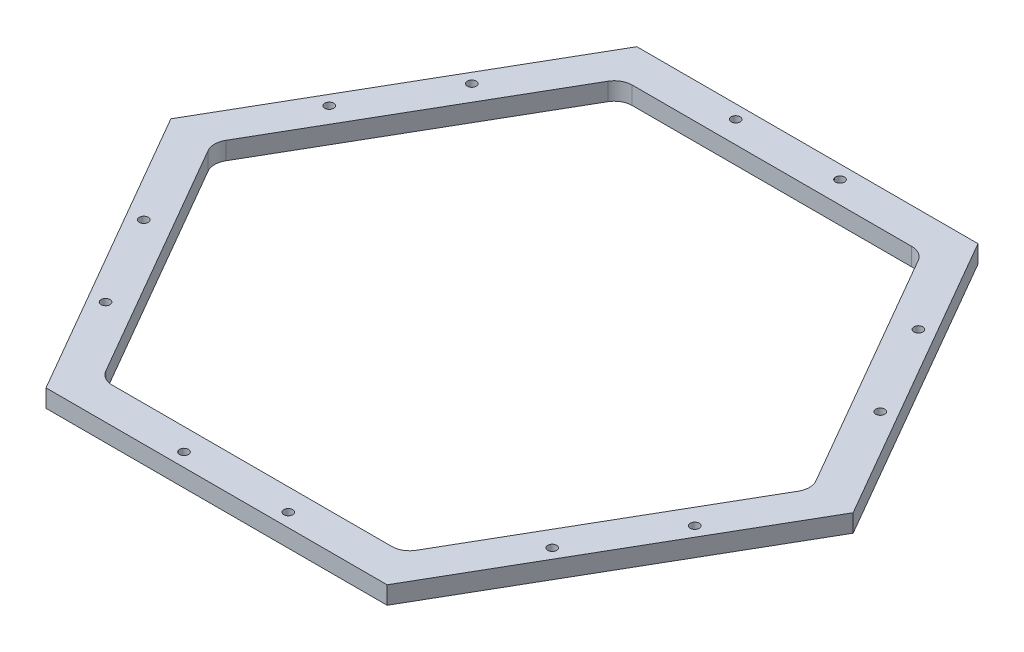
SolidWorks part; units mm, degrees
material "1060 Alloy"
ref_plane "Front Plane" through (0, 0, 0) normal (0, 0, 1) x (1, 0, 0)
ref_plane "Top Plane" through (0, 0, 0) normal (0, 1, 0) x (1, 0, 0)
ref_plane "Right Plane" through (0, 0, 0) normal (1, 0, 0) x (0, 0, -1)
sketch "Sketch1" plane through (0, 0, 0) normal (0, 1, 0) x (1, 0, 0)
  line L0 (60.9985, 0) -> (30.4993, 52.8263)
  line L1 (52.7496, 1.5875) -> (27.7496, 44.8888)
  line L2 (25, 46.4763) -> (-25, 46.4763)
  line L3 (-27.7496, 44.8888) -> (-52.7496, 1.5875)
  line L4 (-52.7496, -1.5875) -> (-27.7496, -44.8888)
  line L5 (-25, -46.4763) -> (25, -46.4763)
  line L6 (27.7496, -44.8888) -> (52.7496, -1.5875)
  line L7 (30.4993, 52.8263) -> (-30.4993, 52.8263)
  line L8 (-30.4993, 52.8263) -> (-60.9985, 0)
  line L9 (-60.9985, 0) -> (-30.4993, -52.8263)
  line L10 (-30.4993, -52.8263) -> (30.4993, -52.8263)
  line L11 (30.4993, -52.8263) -> (60.9985, 0)
  line L12 (-26.8331, 46.4763) -> (-53.6662, 0) construction
  line L13 (-53.6662, 0) -> (-26.8331, -46.4763) construction
  line L14 (-26.8331, -46.4763) -> (26.8331, -46.4763) construction
  line L15 (26.8331, -46.4763) -> (53.6662, 0) construction
  line L16 (53.6662, 0) -> (26.8331, 46.4763) construction
  line L17 (26.8331, 46.4763) -> (-26.8331, 46.4763) construction
  circle A0 centre (0, 0) radius 46.4763 construction
  arc A1 (-52.7496, 1.5875) -> (-52.7496, -1.5875) centre (-50, 0) ccw
  arc A2 (-27.7496, -44.8888) -> (-25, -46.4763) centre (-25, -43.3013) ccw
  arc A3 (25, -46.4763) -> (27.7496, -44.8888) centre (25, -43.3013) ccw
  arc A4 (52.7496, 1.5875) -> (52.7496, -1.5875) centre (50, 0) cw
  arc A5 (27.7496, 44.8888) -> (25, 46.4763) centre (25, 43.3013) ccw
  arc A6 (-25, 46.4763) -> (-27.7496, 44.8888) centre (-25, 43.3013) ccw
  dimension "D2" = 3.175
  dimension "D3" = 50
  dimension "D1" = 6.35
extrude "Boss-Extrude1" add sketch "Sketch1" along normal blind 3.175
hole_wizard "M2x0.4 Tapped Hole1" positions "Sketch3" profile "Sketch2" tap size "M2x0.4" standard "ANSI Metric"
sketch "Sketch3" plane through (0, 3.175, 0) normal (0, 1, 0) x (1, 0, 0)
  point P0 (8.2439, 50.4102)
  point P3 (-10.4188, 50.4102)
sketch "Sketch2" plane through (8.2439, 3.175, -50.4102) normal (1, 0, 0) x (0, 0, 1)
  line L0 (0, 0) -> (0, 6.5767)
  line L1 (0, 6.5767) -> (0.8, 6.096)
  line L2 (0.8, 6.096) -> (0.8, 0)
  line L5 (0.8, 0) -> (0, 0)
  line L10 (0, 6.5767) -> (-0.8, 6.096) construction
  line L11 (0, -6.35) -> (0, 107.95) construction
  dimension "Tap Drill Dia." = 1.6
  dimension "Tap Drill Depth" = 6.096
  dimension "Drill Angle" = 118
cosmetic thread "Hole Thread1" parameters "D1"=3.175, "D2"=2
cosmetic thread "Hole Thread2" parameters "D1"=3.175, "D2"=2
pattern_circular "CirPattern1" count 6 over 360 about axis through (0, 0, 0) along (0, 1, 0) of "M2x0.4 Tapped Hole1"
